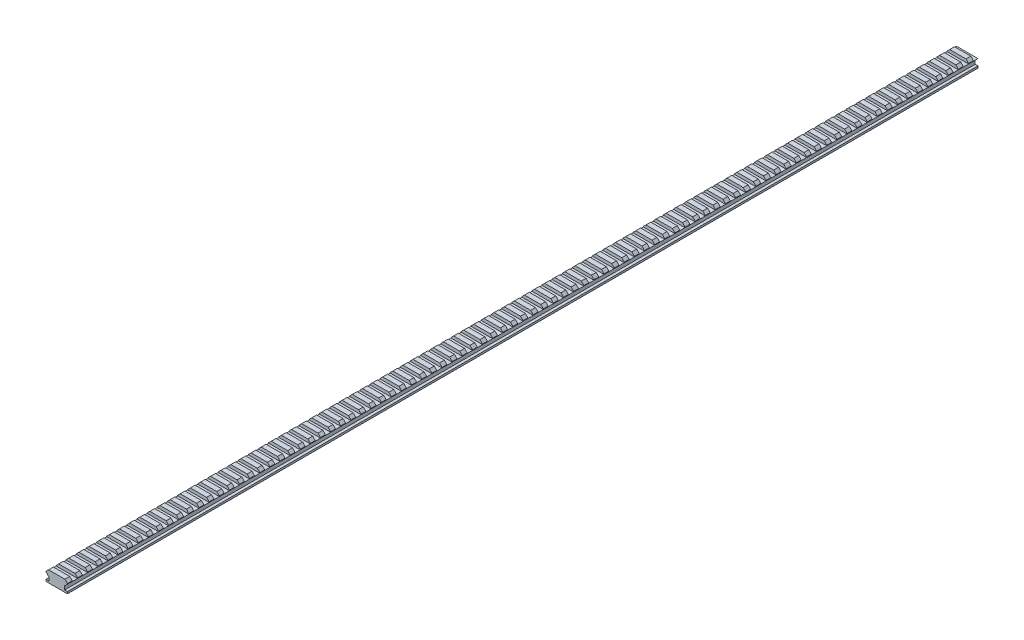
SolidWorks part; units mm, degrees
ref_plane "Front" through (0, 0, 0) normal (0, 0, 1) x (1, 0, 0)
ref_plane "Top" through (0, 0, 0) normal (0, 1, 0) x (1, 0, 0)
ref_plane "Right" through (0, 0, 0) normal (1, 0, 0) x (0, 0, -1)
sketch "Sketch1" plane through (0, 0, 0) normal (0, 0, 1) x (1, 0, 0)
  line L20 (10.6045, -3.0607) -> (10.6045, -2.5273)
  line L21 (-10.6045, -2.5273) -> (-10.6045, -3.0607)
  line L22 (10.6045, -2.5273) -> (8.0772, 0)
  line L23 (8.0772, -5.588) -> (7.8359, -5.588)
  line L24 (-7.8359, -9.3218) -> (-7.8359, -5.588)
  line L25 (-10.6045, -9.3218) -> (-10.6045, -11.2436)
  line L26 (-10.6045, -11.2436) -> (10.6045, -11.2436)
  line L27 (-7.8359, -5.588) -> (-8.0772, -5.588)
  line L28 (8.0772, 0) -> (-8.0772, 0)
  line L29 (10.6045, -3.0607) -> (8.0772, -5.588)
  line L30 (10.6045, -11.2436) -> (10.6045, -9.3218)
  line L31 (-10.6045, -9.3218) -> (-7.8359, -9.3218)
  line L32 (-10.6045, -2.794) -> (10.6045, -2.794) construction
  line L33 (-8.0772, -5.588) -> (-10.6045, -3.0607)
  line L34 (7.8359, -9.3218) -> (7.8359, -5.588)
  line L35 (7.8359, -9.3218) -> (10.6045, -9.3218)
  line L36 (-8.0772, 0) -> (-10.6045, -2.5273)
extrude "Boss-Extrude1" add sketch "Sketch1" against normal blind 900
ref_plane "Plane1" through (10.6045, 0, 0) normal (1, 0, 0) x (0, 0, -1)
sketch "Sketch2" plane through (10.6045, 0, 0) normal (1, 0, 0) x (0, 0, -1)
  line L2 (900, 0) -> (0, 0) construction
  line L18 (10.0076, 0) -> (4.7752, 0)
  line L32 (10.0076, 0) -> (10.0076, -3.0607)
  line L34 (900, -3.0607) -> (0, -3.0607) construction
  line L35 (10.0076, -3.0607) -> (4.7752, -3.0607)
  line L36 (4.7752, 0) -> (4.7752, -3.0607)
extrude "Cut-Extrude1" cut sketch "Sketch2" against normal through all contours L36 L35 L32 L18
ref_plane "Plane2" through (0, 0, 0) normal (0, 1, 0) x (1, 0, 0)
sketch "Sketch4" plane through (0, 0, 0) normal (0, 1, 0) x (1, 0, 0)
  line L0 (0, 0) -> (0, 900) construction
  line L3 (8.0772, 900) -> (-8.0772, 900) construction
  point P4 (0, 0)
  dimension "D1" = 900
pattern_linear "LPattern2" count 90 spacing 10.0076 along (0, 0, -1) of "Cut-Extrude1"
